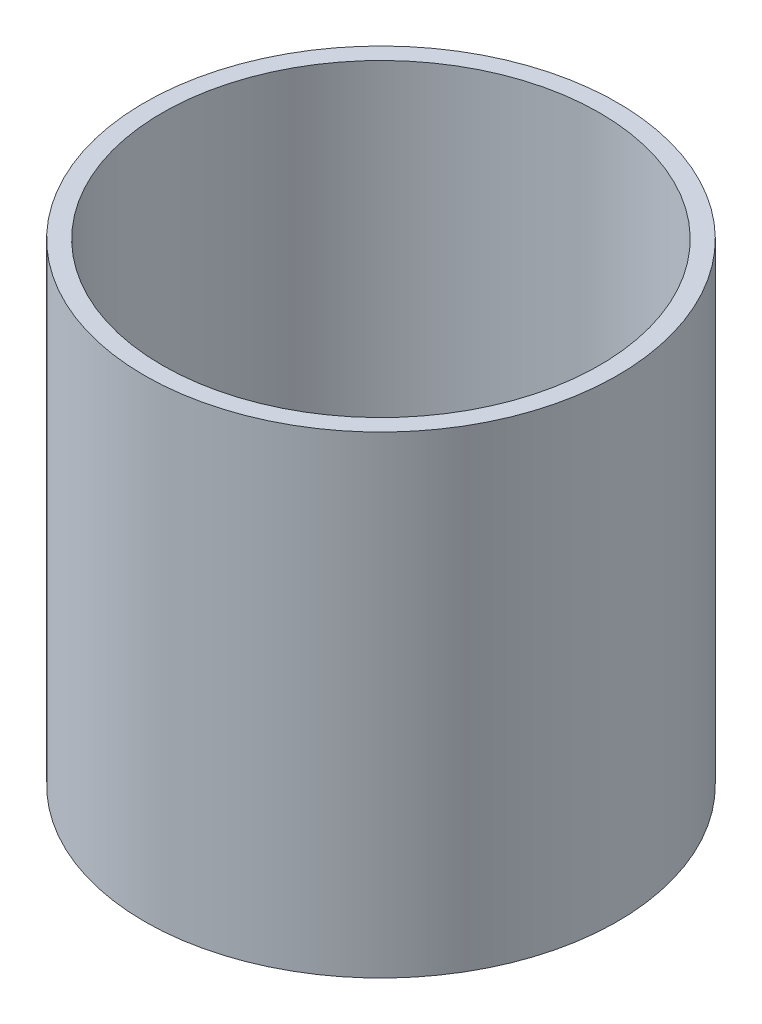
SolidWorks part; units mm, degrees
ref_plane "Plan de face" through (0, 0, 0) normal (0, 0, 1) x (1, 0, 0)
ref_plane "Plan de dessus" through (0, 0, 0) normal (0, 1, 0) x (1, 0, 0)
ref_plane "Plan de droite" through (0, 0, 0) normal (1, 0, 0) x (0, 0, -1)
sketch "Esquisse1" plane through (0, 0, 0) normal (0, 1, 0) x (1, 0, 0)
  circle A0 centre (0, 0) radius 40
  dimension "D1" = 80
extrude "Extrusion1" add sketch "Esquisse1" along normal blind 5
sketch "Esquisse2" plane through (0, 5, 0) normal (0, 1, 0) x (1, 0, 0)
  circle A0 centre (0, 0) radius 40
  circle A1 centre (0, 0) radius 37
  circle A2 centre (0, 0) radius 40 construction
  dimension "D1" = 74
extrude "Extrusion2" add sketch "Esquisse2" along normal blind 75
